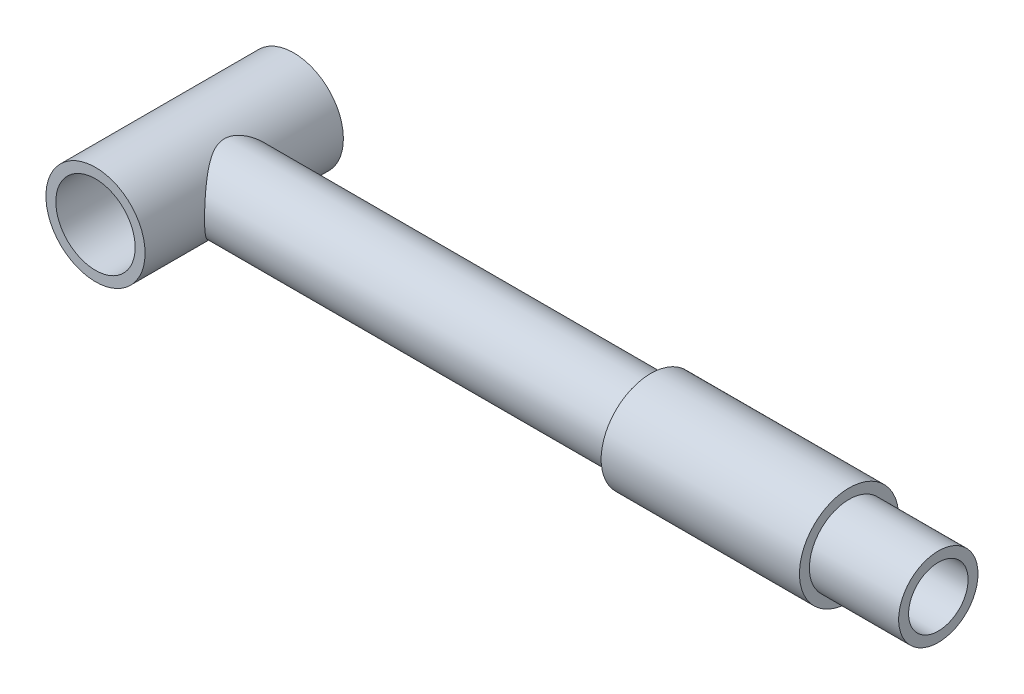
SolidWorks part; units mm, degrees
ref_plane "Ön Düzlem" through (0, 0, 0) normal (0, 0, 1) x (1, 0, 0)
ref_plane "Üst Düzlem" through (0, 0, 0) normal (0, 1, 0) x (1, 0, 0)
ref_plane "Sağ Düzlem" through (0, 0, 0) normal (1, 0, 0) x (0, 0, -1)
sketch "Çizim1" plane through (0, 0, 0) normal (0, 0, 1) x (1, 0, 0)
  circle A0 centre (0, 0) radius 2
  circle A1 centre (0, 0) radius 2.5
  dimension "D1" = 4
  dimension "D2" = 5
extrude "Yükseklik-Ekstrüzyon1" add sketch "Çizim1" along normal mid plane 10
ref_plane "Düzlem1" through (2.5, 0, 0) normal (1, 0, 0) x (0, 0, -1)
sketch "Çizim2" plane through (2.5, 0, 0) normal (1, 0, 0) x (0, 0, -1)
  circle A0 centre (0, 0) radius 2
  circle A1 centre (0, 0) radius 1.5
  dimension "D1" = 4
  dimension "D2" = 3
extrude "Yükseklik-Ekstrüzyon2" add sketch "Çizim2" along normal blind 35 and the other way up to surface
ref_plane "Düzlem2" through (32.9977, 0, 0) normal (1, 0, 0) x (0, 0, -1)
sketch "Çizim3" plane through (32.9977, 0, 0) normal (1, 0, 0) x (0, 0, -1)
  circle A0 centre (0, 0) radius 2.5
  circle A1 centre (0, 0) radius 2 construction
  circle A2 centre (0, 0) radius 2
  dimension "D1" = 5
extrude "Yükseklik-Ekstrüzyon3" add sketch "Çizim3" against normal blind 10
